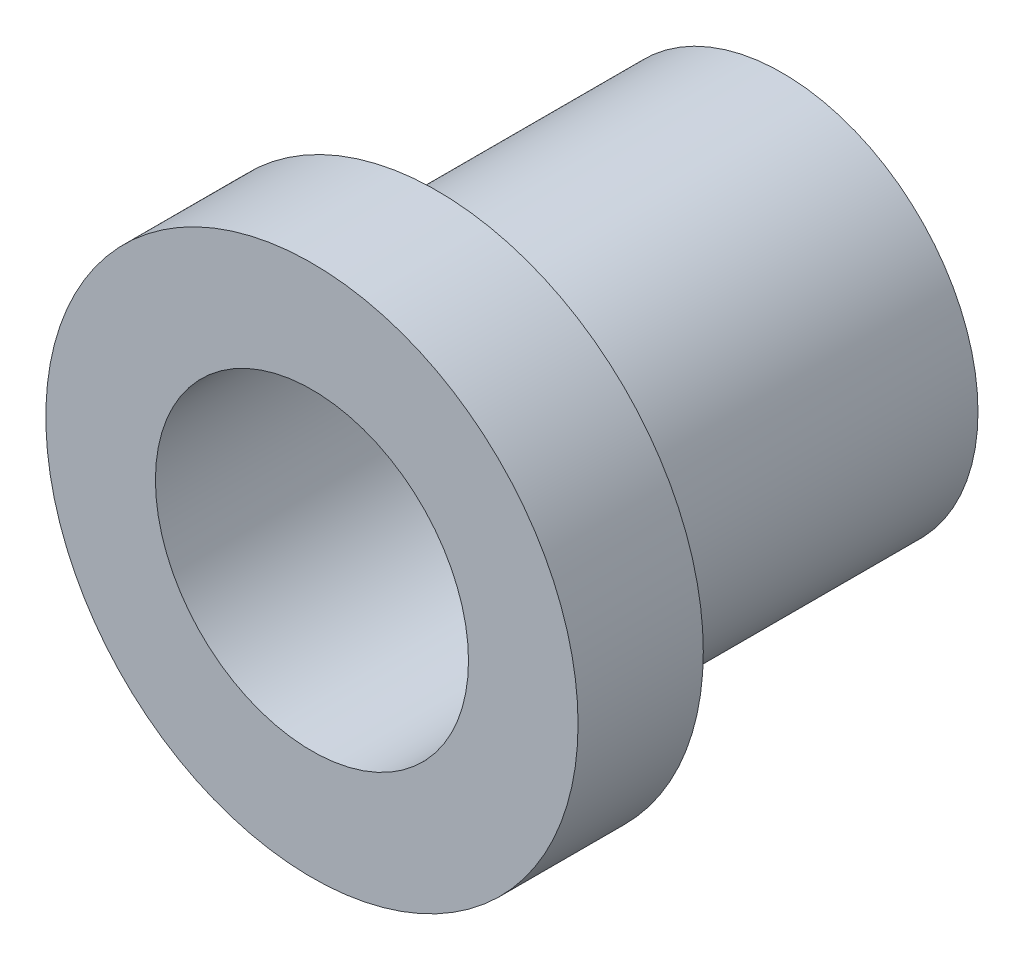
SolidWorks part; units mm, degrees
ref_plane "Front Plane" through (0, 0, 0) normal (0, 0, 1) x (1, 0, 0)
ref_plane "Top Plane" through (0, 0, 0) normal (0, 1, 0) x (1, 0, 0)
ref_plane "Right Plane" through (0, 0, 0) normal (1, 0, 0) x (0, 0, -1)
sketch "Sketch1" plane through (0, 0, 0) normal (0, 0, 1) x (1, 0, 0)
  circle A0 centre (0, 0) radius 5.3975
  circle A1 centre (0, 0) radius 3.175
  dimension "D1" = 10.795
  dimension "D2" = 6.35
extrude "Boss-Extrude1" add sketch "Sketch1" along normal blind 2.54
sketch "Sketch2" plane through (0, 0, 0) normal (0, 0, -1) x (-1, 0, 0)
  circle A0 centre (0, 0) radius 3.175
  circle A1 centre (0, 0) radius 3.9688
  dimension "D1" = 6.35
  dimension "D2" = 7.9375
extrude "Boss-Extrude2" add sketch "Sketch2" along normal blind 7
